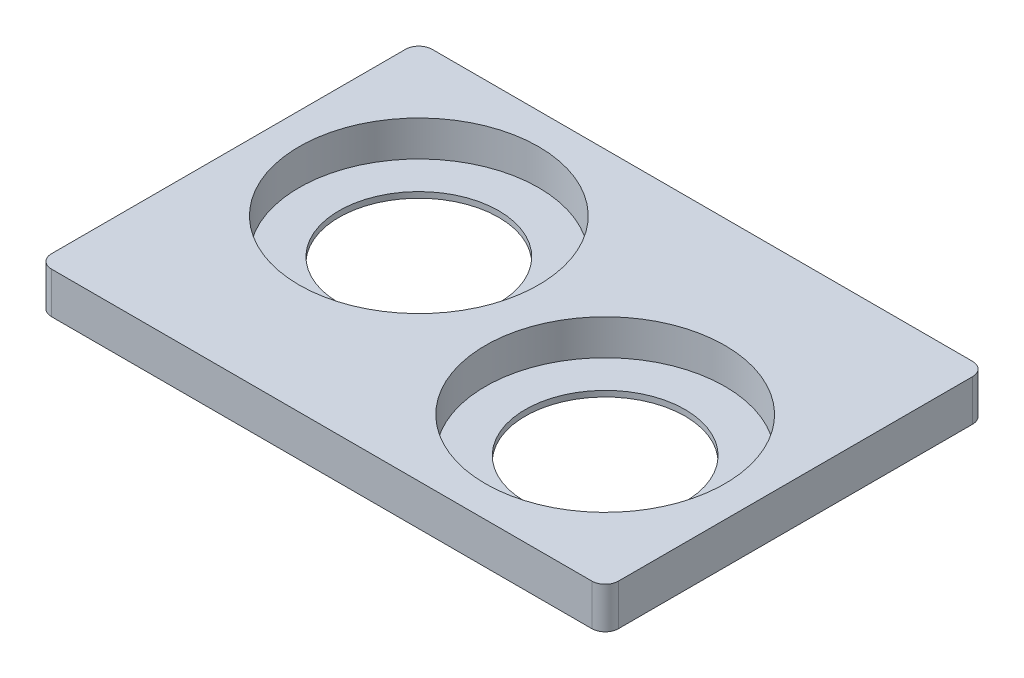
SolidWorks part; units mm, degrees
ref_plane "Front Plane" through (0, 0, 0) normal (0, 0, 1) x (1, 0, 0)
ref_plane "Top Plane" through (0, 0, 0) normal (0, 1, 0) x (1, 0, 0)
ref_plane "Right Plane" through (0, 0, 0) normal (1, 0, 0) x (0, 0, -1)
sketch "Sketch1" plane through (0, 0, 0) normal (0, 1, 0) x (1, 0, 0)
  line L1 (0, 0) -> (127.8, 0)
  line L2 (0, 0) -> (0, -85.8)
  line L3 (0, -85.8) -> (127.8, -85.8)
  line L4 (127.8, 0) -> (127.8, -85.8)
  dimension "D1" = 127.8
  dimension "D2" = 85.8
extrude "Boss-Extrude1" add sketch "Sketch1" along normal blind 9.3
sketch "Sketch2" plane through (0, 9.3, 0) normal (0, 1, 0) x (1, 0, 0)
  line L0 (127.8, 0) -> (0, 0) construction
  line L1 (0, 0) -> (0, -85.8) construction
  line L2 (127.8, -85.8) -> (127.8, 0) construction
  line L3 (0, -85.8) -> (127.8, -85.8) construction
  circle A0 centre (93.8, -51.8) radius 27
  circle A1 centre (34, -34) radius 27
  point P2 (97.0862, -53.8734)
  point P5 (34.5711, -30.7295)
  point P6 (93.2289, -52.9423)
  point P7 (0, 0)
  dimension "D1" = 54
  dimension "D2" = 34
  dimension "D3" = 34
  dimension "D4" = 34
  dimension "D5" = 34
extrude "Cut-Extrude1" cut sketch "Sketch2" against normal blind 8
sketch "Sketch3" plane through (0, 1.3, 0) normal (0, 1, 0) x (1, 0, 0)
  circle A0 centre (93.8, -51.8) radius 18
  circle A1 centre (34, -34) radius 18
  dimension "D1" = 36
extrude "Cut-Extrude2" cut sketch "Sketch3" against normal blind 9
fillet "Fillet1" radius 3 4 edges at (0, 4.65, 85.8) (0, 4.65, 0) (127.8, 4.65, 0) (127.8, 4.65, 85.8)
sketch "Sketch4" plane through (0, 0, 0) normal (0, -1, 0) x (1, 0, 0)
  line L0 (52, 2) -> (124.8, 2)
  line L1 (125.8, 3) -> (125.8, 33.8)
  line L2 (75.8, 83.8) -> (3, 83.8)
  line L3 (2, 82.8) -> (2, 52)
  line L4 (0, 82.8) -> (0, 3)
  line L5 (124.8, 85.8) -> (3, 85.8)
  line L6 (127.8, 3) -> (127.8, 82.8)
  line L7 (3, 0) -> (124.8, 0)
  line L8 (3, 2) -> (124.8, 2) construction
  line L9 (0, 82.8) -> (0, 3) construction
  line L10 (124.8, 83.8) -> (3, 83.8) construction
  line L11 (3, 0) -> (124.8, 0) construction
  line L12 (125.3, 83.3) -> (125.3, 65.3)
  line L13 (125.3, 65.3) -> (121.8, 65.3)
  line L14 (125.8, 3) -> (125.8, 2)
  line L15 (125.8, 2) -> (124.8, 2)
  line L16 (2, 82.8) -> (2, 3) construction
  line L17 (2.5, 20.5) -> (2.5, 2.5)
  line L18 (3, 83.8) -> (2, 83.8)
  line L19 (2, 83.8) -> (2, 82.8)
  line L20 (52, 2) -> (52, 11)
  line L21 (2, 52) -> (11, 52)
  line L22 (75.8, 83.8) -> (75.8, 74.8)
  line L23 (125.8, 33.8) -> (116.8, 33.8)
  line L24 (125.8, 3) -> (125.8, 82.8) construction
  line L25 (127.8, 3) -> (127.8, 82.8) construction
  line L26 (124.8, 85.8) -> (3, 85.8) construction
  line L27 (2.5, 2.5) -> (20.5, 2.5)
  line L28 (20.5, 2.5) -> (20.5, 6)
  line L29 (20.5, 6) -> (6, 20.5)
  line L30 (6, 20.5) -> (2.5, 20.5)
  line L31 (0, 3) -> (0, 82.8) construction
  line L32 (121.8, 65.3) -> (107.3, 79.8)
  line L33 (107.3, 79.8) -> (107.3, 83.3)
  line L34 (107.3, 83.3) -> (125.3, 83.3)
  line L35 (3, 85.8) -> (124.8, 85.8) construction
  line L38 (127.8, 82.8) -> (127.8, 3) construction
  circle A2 centre (34, 34) radius 27 construction
  circle A3 centre (93.8, 51.8) radius 27 construction
  arc A4 (52, 11) -> (11, 52) centre (34, 34) ccw
  arc A5 (75.8, 74.8) -> (116.8, 33.8) centre (93.8, 51.8) ccw
  arc A8 (3, 85.8) -> (0, 82.8) centre (3, 82.8) ccw
  arc A9 (127.8, 82.8) -> (124.8, 85.8) centre (124.8, 82.8) ccw
  arc A10 (124.8, 0) -> (127.8, 3) centre (124.8, 3) ccw
  arc A11 (0, 3) -> (3, 0) centre (3, 3) ccw
  arc A12 (3, 85.8) -> (0, 82.8) centre (3, 82.8) ccw construction
  arc A14 (124.8, 0) -> (127.8, 3) centre (124.8, 3) ccw construction
  arc A15 (0, 3) -> (3, 0) centre (3, 3) ccw construction
  arc A16 (2, 3) -> (3, 2) centre (3, 3) ccw construction
  arc A17 (124.8, 2) -> (125.8, 3) centre (124.8, 3) ccw construction
  arc A18 (125.8, 82.8) -> (124.8, 83.8) centre (124.8, 82.8) ccw construction
  arc A19 (3, 83.8) -> (2, 82.8) centre (3, 82.8) ccw construction
  arc A21 (127.8, 82.8) -> (124.8, 85.8) centre (124.8, 82.8) ccw construction
  point P54 (0, 0)
  dimension "D4" = 50
  dimension "D5" = 50
  dimension "D6" = 50
  dimension "D7" = 50
  dimension "D3" = 9
  dimension "D8" = 9
  dimension "D9" = 2.5
  dimension "D10" = 3.5
  dimension "D11" = 3.5
  dimension "D12" = 18
  dimension "D13" = 18
  dimension "D14" = 2.5
  dimension "D15" = 2.5
  dimension "D16" = 2.5
  dimension "D17" = 18
  dimension "D18" = 18
  dimension "D19" = 3.5
  dimension "D20" = 3.5
  dimension "D1" = 0
  dimension "D2" = 2
extrude "Cut-Extrude3" cut sketch "Sketch4" against normal blind 8
fillet "Fillet2" radius 2 10 edges at (2.5, 4, 20.5) (6, 4, 20.5) (20.5, 4, 6) (20.5, 4, 2.5) (121.8, 4, 65.3) (125.3, 4, 65.3) (107.3, 4, 79.8) (107.3, 4, 83.3) (125.3, 4, 83.3) (2.5, 4, 2.5)
fillet "Fillet3" radius 3.5 10 edges at (2, 4, 83.8) (2, 4, 52) (11, 4, 52) (52, 4, 11) (52, 4, 2) (125.8, 4, 2) (116.8, 4, 33.8) (125.8, 4, 33.8) (75.8, 4, 74.8) (75.8, 4, 83.8)
